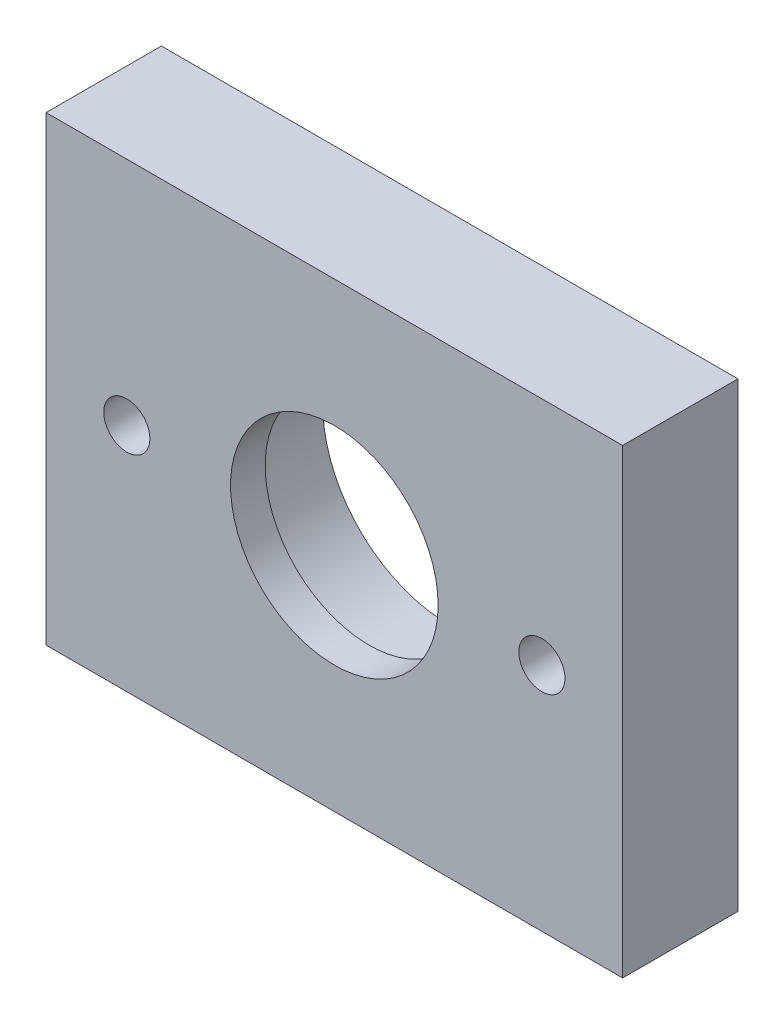
SolidWorks part; units mm, degrees
material "ABS"
ref_plane "Front Plane" through (0, 0, 0) normal (0, 0, 1) x (1, 0, 0)
ref_plane "Top Plane" through (0, 0, 0) normal (0, 1, 0) x (1, 0, 0)
ref_plane "Right Plane" through (0, 0, 0) normal (1, 0, 0) x (0, 0, -1)
sketch "Sketch1" plane through (0, 0, 0) normal (0, 0, 1) x (1, 0, 0)
  line L0 (0, 0) -> (0, 20) construction
  line L1 (-25, -20) -> (25, -20)
  line L2 (-25, -20) -> (-25, 20)
  line L3 (-25, 20) -> (25, 20)
  line L4 (25, -20) -> (25, 20)
  line L5 (-25, -20) -> (25, 20) construction
  line L6 (-25, 20) -> (25, -20) construction
  circle A0 centre (0, 0) radius 11
  circle A1 centre (-18, 0) radius 2
  circle A2 centre (18, 0) radius 2
  point P0 (0, 0)
  dimension "D3" = 22
  dimension "D4" = 4
  dimension "D5" = 20
  dimension "D6" = 18
  dimension "D1" = 50
  dimension "D2" = 40
extrude "Boss-Extrude1" add sketch "Sketch1" along normal blind 10
sketch "Sketch2" plane through (0, 0, 10) normal (0, 0, 1) x (1, 0, 0)
  circle A0 centre (0, 0) radius 9
  circle A1 centre (0, 0) radius 11
  dimension "D1" = 18
  dimension "D2" = 22
extrude "Boss-Extrude2" add sketch "Sketch2" against normal blind 3
